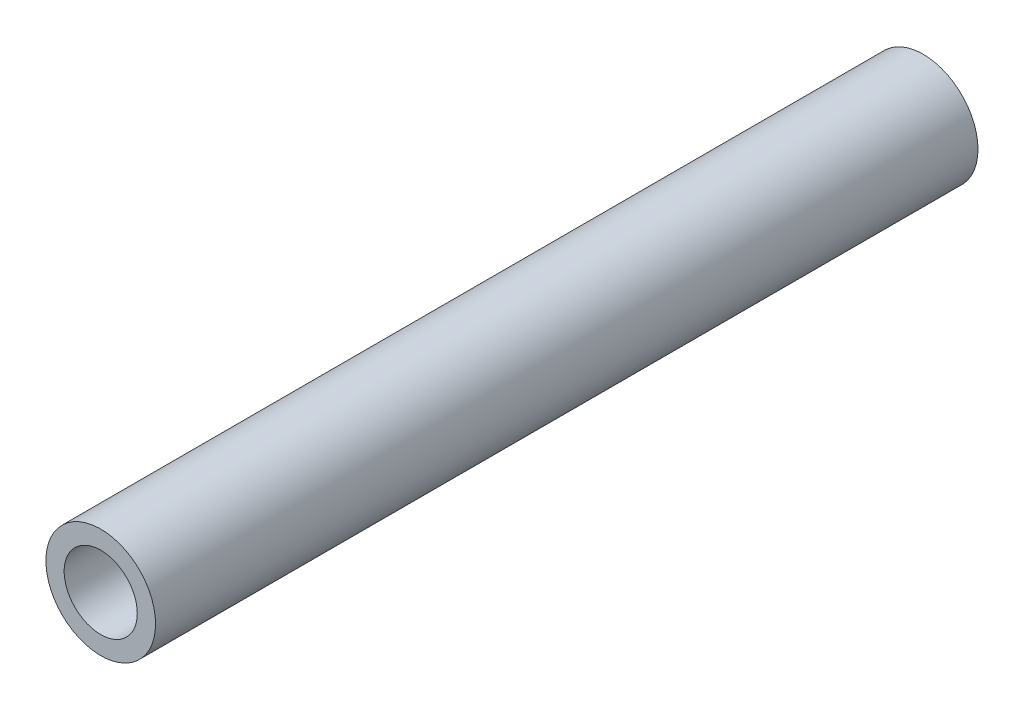
SolidWorks part; units mm, degrees
ref_plane "前视基准面" through (0, 0, 0) normal (0, 0, 1) x (1, 0, 0)
ref_plane "上视基准面" through (0, 0, 0) normal (0, 1, 0) x (1, 0, 0)
ref_plane "右视基准面" through (0, 0, 0) normal (1, 0, 0) x (0, 0, -1)
sketch "草图1" plane through (0, 0, 0) normal (0, 0, 1) x (1, 0, 0)
  circle A0 centre (0, 0) radius 3
  circle A1 centre (0, 0) radius 2
  dimension "D1" = 4
  dimension "D2" = 6
extrude "凸台-拉伸1" add sketch "草图1" along normal mid plane 45
